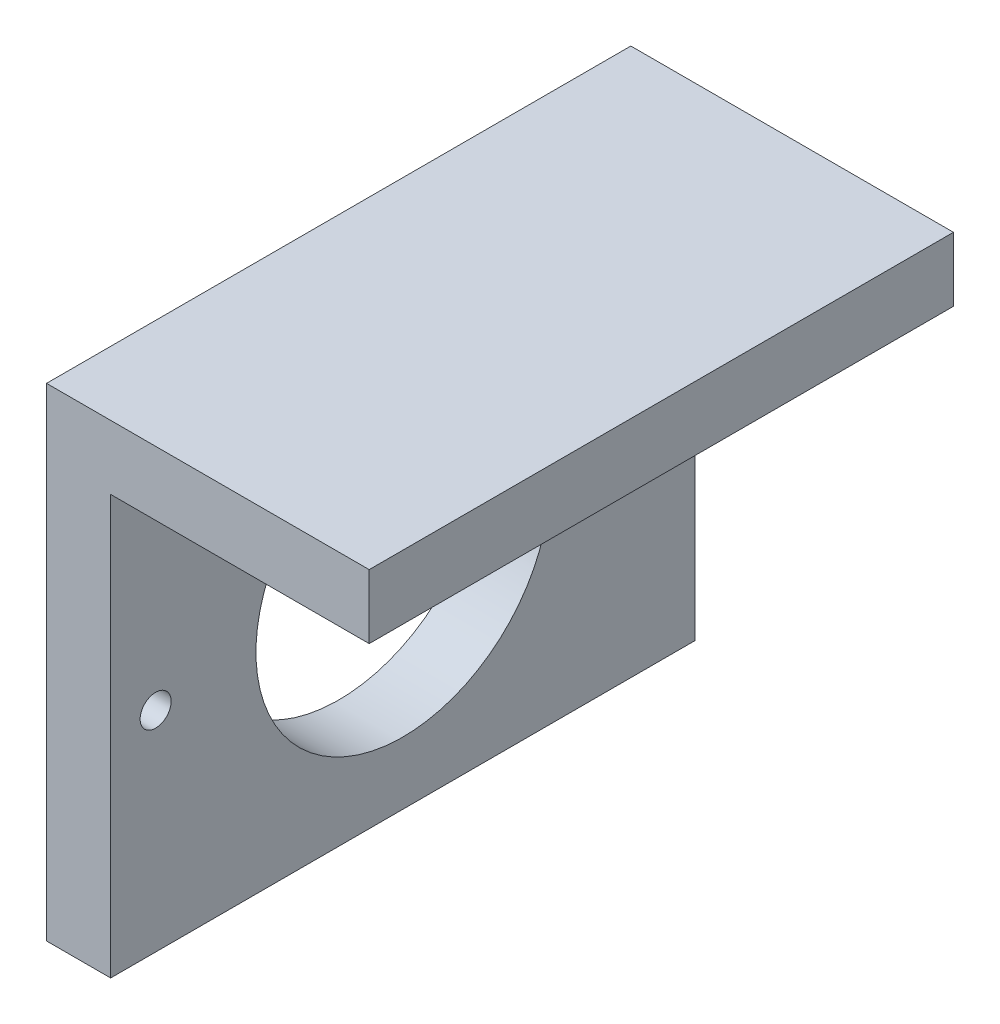
SolidWorks part; units mm, degrees
ref_plane "Front Plane" through (0, 0, 0) normal (0, 0, 1) x (1, 0, 0)
ref_plane "Top Plane" through (0, 0, 0) normal (0, 1, 0) x (1, 0, 0)
ref_plane "Right Plane" through (0, 0, 0) normal (1, 0, 0) x (0, 0, -1)
sketch "Sketch3" plane through (0, 0, 0) normal (1, 0, 0) x (0, 0, -1)
  line L1 (0, 0) -> (56.5, 0)
  line L2 (0, 0) -> (0, 46.7)
  line L3 (0, 46.7) -> (56.5, 46.7)
  line L4 (56.5, 0) -> (56.5, 46.7)
  circle A1 centre (28.25, 20.25) radius 14.2
  circle A2 centre (4.35, 20.25) radius 1.5
  circle A3 centre (52.15, 20.25) radius 1.5
  point P5 (28.25, 20.25)
  point P12 (4.35, 20.25)
  point P13 (52.15, 20.25)
  dimension "D3" = 28.25
  dimension "D1" = 56.5
  dimension "D2" = 46.7
  dimension "D4" = 20.25
extrude "Boss-Extrude1" add sketch "Sketch3" along normal blind 6.2
sketch "Sketch4" plane through (6.2, 0, 0) normal (1, 0, 0) x (0, 0, -1)
  line L0 (0, 46.7) -> (56.5, 46.7) construction
  line L1 (0, 46.7) -> (56.5, 46.7)
  line L2 (0, 46.7) -> (0, 40.5)
  line L3 (0, 40.5) -> (56.5, 40.5)
  line L4 (56.5, 46.7) -> (56.5, 40.5)
  line L5 (0, 55) -> (0, -55) construction
  line L6 (56.5, 0) -> (56.5, 46.7) construction
  dimension "D1" = 6.2
extrude "Boss-Extrude2" add sketch "Sketch4" along normal blind 25
